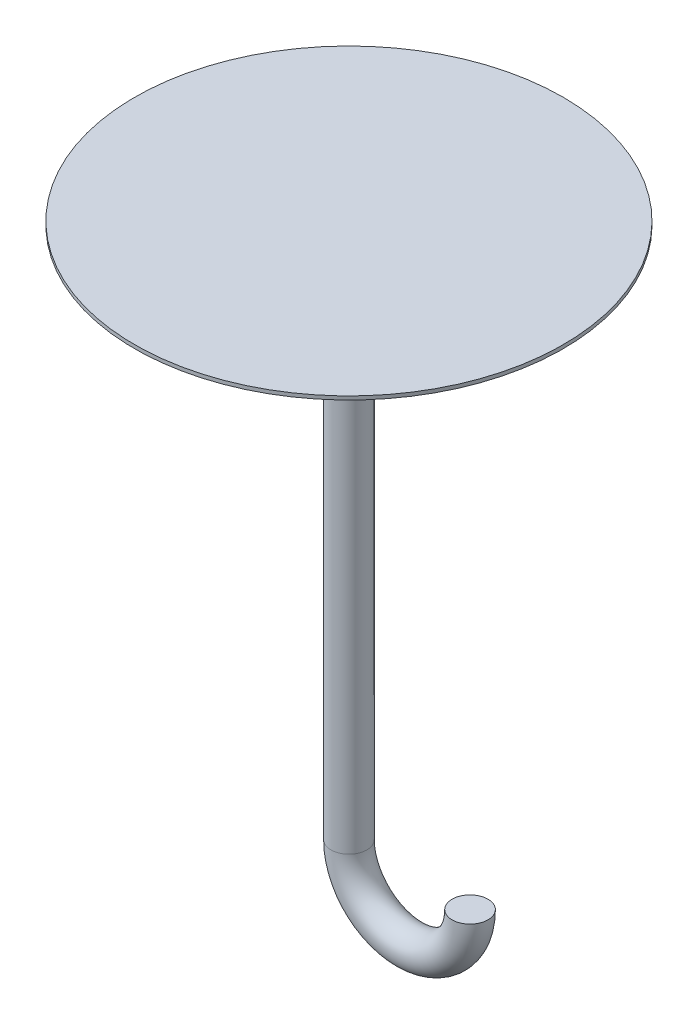
SolidWorks part; units mm, degrees
ref_plane "Front Plane" through (0, 0, 0) normal (0, 0, 1) x (1, 0, 0)
ref_plane "Top Plane" through (0, 0, 0) normal (0, 1, 0) x (1, 0, 0)
ref_plane "Right Plane" through (0, 0, 0) normal (1, 0, 0) x (0, 0, -1)
sketch "Sketch1" plane through (0, 0, 0) normal (0, 0, 1) x (1, 0, 0)
  line L0 (0, 68.3737) -> (0, -81.6263)
  arc A0 (0, -81.6263) -> (23.8706, -81.6263) centre (11.9353, -81.6263) ccw
ref_plane "Plane1" through (0, 68.3737, 0) normal (0, -1, 0) x (-1, 0, 0)
sketch "Sketch5" plane through (0, 68.3737, 0) normal (0, -1, 0) x (-1, 0, 0)
  circle A0 centre (5.0176, -0.0052) radius 5.0176
sweep "Sweep2" add profiles "Sketch5" path "Sketch1"
sketch "Sketch8" plane through (0, 68.3737, 0) normal (0, -1, 0) x (-1, 0, 0)
  circle A0 centre (5.0176, -0.0052) radius 60
  dimension "D1" = 120
extrude "Boss-Extrude3" add sketch "Sketch8" along normal blind 1
